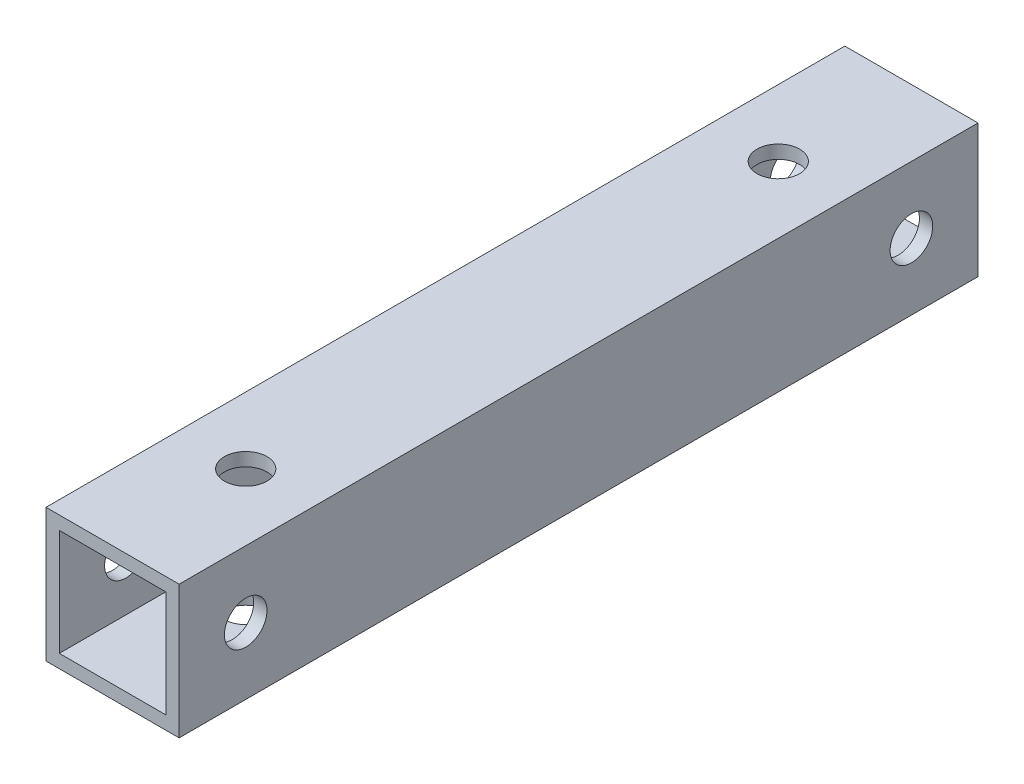
SolidWorks part; units mm, degrees
ref_plane "正面" through (0, 0, 0) normal (0, 0, 1) x (1, 0, 0)
ref_plane "平面" through (0, 0, 0) normal (0, 1, 0) x (1, 0, 0)
ref_plane "右側面" through (0, 0, 0) normal (1, 0, 0) x (0, 0, -1)
sketch "ｽｹｯﾁ1" plane through (0, 0, 0) normal (0, 0, 1) x (1, 0, 0)
  line L1 (-5, -5) -> (5, -5)
  line L2 (-5, -5) -> (-5, 5)
  line L3 (-5, 5) -> (5, 5)
  line L4 (5, -5) -> (5, 5)
  line L5 (-5, -5) -> (5, 5) construction
  line L6 (-5, 5) -> (5, -5) construction
  line L7 (-4, -4) -> (4, -4)
  line L8 (-4, -4) -> (-4, 4)
  line L9 (-4, 4) -> (4, 4)
  line L10 (4, -4) -> (4, 4)
  line L11 (-4, -4) -> (4, 4) construction
  line L12 (-4, 4) -> (4, -4) construction
  point P0 (0, 0)
  point P6 (0, 0)
  dimension "D1" = 10
  dimension "D2" = 10
  dimension "D3" = 1
extrude "ﾎﾞｽ - 押し出し1" add sketch "ｽｹｯﾁ1" along normal mid plane 60
sketch "ｽｹｯﾁ3" plane through (5, 0, 0) normal (1, 0, 0) x (0, 0, -1)
  line L0 (30, -5) -> (30, 5) construction
  line L1 (-30, -5) -> (-30, 5) construction
  circle A0 centre (-25, 0) radius 1.6
  circle A1 centre (25, 0) radius 1.6
  dimension "D1" = 3.2
  dimension "D2" = 5
  dimension "D3" = 5
extrude "ｶｯﾄ - 押し出し1" cut sketch "ｽｹｯﾁ3" against normal through all
sketch "ｽｹｯﾁ4" plane through (0, 5, 0) normal (0, 1, 0) x (1, 0, 0)
  line L0 (5, 30) -> (-5, 30) construction
  line L1 (5, -30) -> (-5, -30) construction
  circle A0 centre (0, -20) radius 1.6
  circle A1 centre (0, 20) radius 1.6
  dimension "D1" = 3.2
  dimension "D2" = 10
  dimension "D3" = 10
extrude "ｶｯﾄ - 押し出し2" cut sketch "ｽｹｯﾁ4" against normal through all
